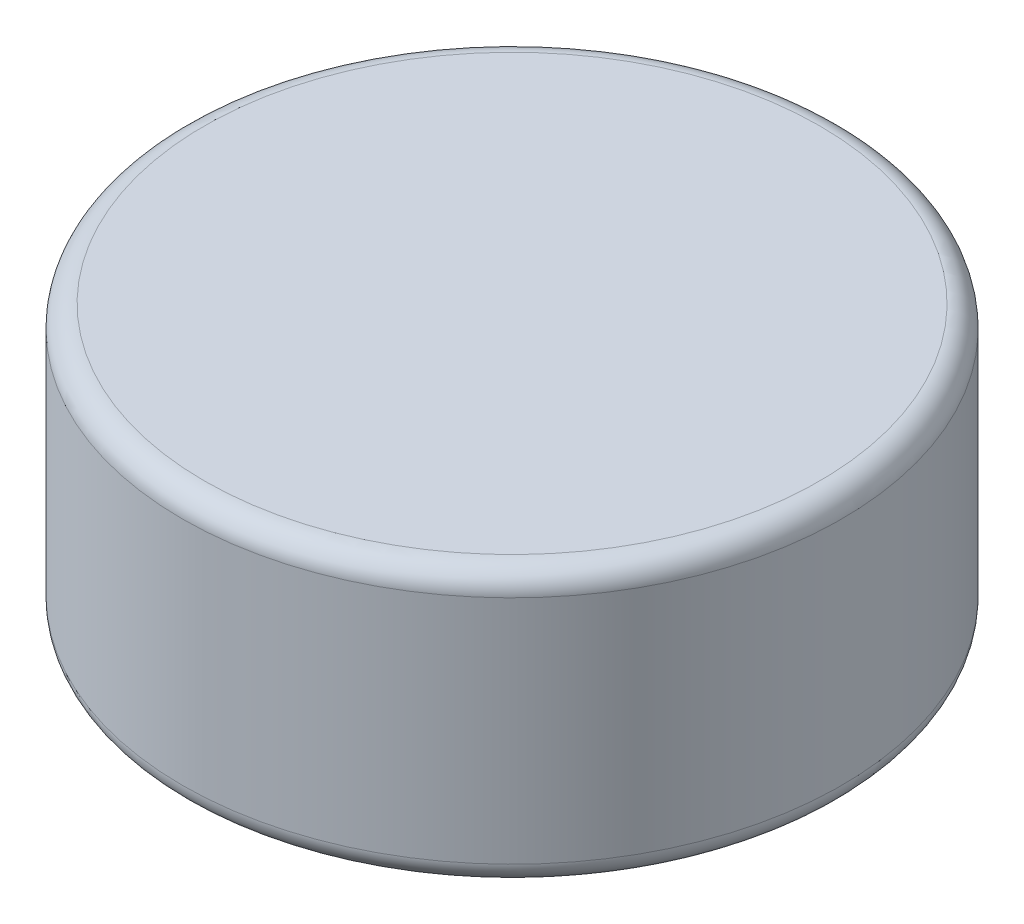
SolidWorks part; units mm, degrees
ref_plane "Front Plane" through (0, 0, 0) normal (0, 0, 1) x (1, 0, 0)
ref_plane "Top Plane" through (0, 0, 0) normal (0, 1, 0) x (1, 0, 0)
ref_plane "Right Plane" through (0, 0, 0) normal (1, 0, 0) x (0, 0, -1)
sketch "Sketch1" plane through (0, 0, 0) normal (0, 1, 0) x (1, 0, 0)
  circle A0 centre (0, 0) radius 3
  dimension "D1" = 6
extrude "Boss-Extrude1" add sketch "Sketch1" along normal mid plane 2.5
fillet "Fillet1" radius 0.2 2 edges at (0, -1.25, 3) (0, 1.25, 3)
